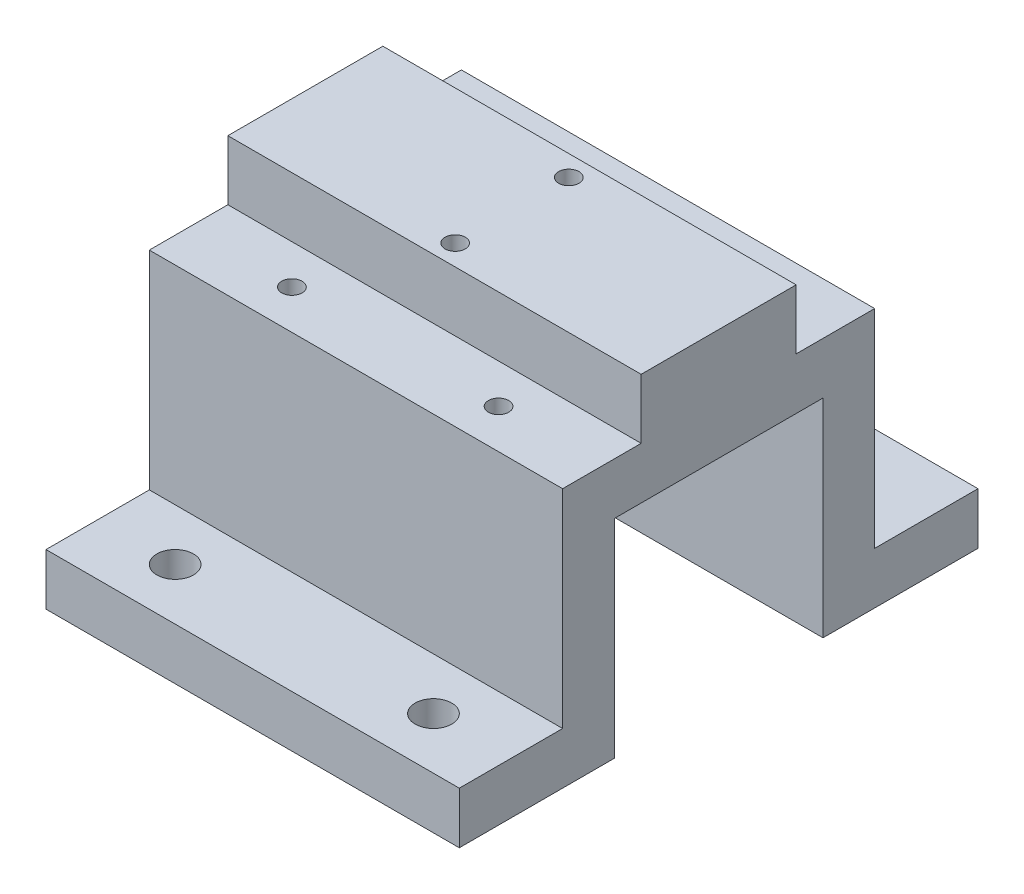
SolidWorks part; units mm, degrees
ref_plane "Front Plane" through (0, 0, 0) normal (0, 0, 1) x (1, 0, 0)
ref_plane "Top Plane" through (0, 0, 0) normal (0, 1, 0) x (1, 0, 0)
ref_plane "Right Plane" through (0, 0, 0) normal (1, 0, 0) x (0, 0, -1)
sketch "Sketch1" plane through (0, 0, 0) normal (1, 0, 0) x (0, 0, -1)
  line L0 (0, 0) -> (0, 51.054) construction
  line L1 (19.177, 31.877) -> (-19.177, 31.877)
  line L2 (-19.177, 31.877) -> (-19.177, 0)
  line L3 (-19.177, 0) -> (-12.827, 0)
  line L4 (-12.827, 0) -> (-12.827, 25.527)
  line L5 (-12.827, 25.527) -> (12.827, 25.527)
  line L6 (0, 25.527) -> (0, 31.877)
  line L7 (31.877, 0) -> (31.877, 6.35)
  line L8 (-19.177, 0) -> (-31.877, 0)
  line L9 (-19.177, 0) -> (-19.177, 6.35)
  line L10 (-19.177, 6.35) -> (-31.877, 6.35)
  line L11 (-31.877, 0) -> (-31.877, 6.35)
  line L12 (19.177, 6.35) -> (31.877, 6.35)
  line L13 (19.177, 0) -> (19.177, 6.35)
  line L14 (19.177, 0) -> (31.877, 0)
  line L15 (12.827, 0) -> (12.827, 25.527)
  line L16 (19.177, 0) -> (12.827, 0)
  line L17 (19.177, 31.877) -> (19.177, 0)
  dimension "D1" = 25.527
  dimension "D2" = 6.35
  dimension "D3" = 6.35
  dimension "D4" = 12.827
  dimension "D5" = 6.35
  dimension "D6" = 12.7
extrude "Boss-Extrude1" add sketch "Sketch1" along normal blind 50.8 contours L17 L1 L6 L5 L15 L16 L13 | L13 L14 L7 L12 | L5 L6 L1 L2 L3 L4 | L11 L8 L2 L10
sketch "Sketch2" plane through (0, 31.877, 0) normal (0, 1, 0) x (1, 0, 0)
  line L0 (0, 0) -> (50.8, 0) construction
  line L1 (0, 19.177) -> (0, -19.177) construction
  line L2 (50.8, 19.177) -> (50.8, -19.177) construction
  line L4 (50.8, -9.525) -> (0, -9.525)
  line L5 (50.8, -9.525) -> (50.8, 9.525)
  line L6 (50.8, 9.525) -> (0, 9.525)
  line L7 (0, -9.525) -> (0, 9.525)
  line L8 (50.8, -9.525) -> (0, 9.525) construction
  line L9 (50.8, 9.525) -> (0, -9.525) construction
  point P6 (25.4, 0)
  dimension "D1" = 19.05
extrude "Boss-Extrude2" add sketch "Sketch2" along normal blind 7.3508
hole_wizard "M3x0.5 Tapped Hole1" positions "Sketch3" profile "Sketch5" tap size "M3x0.5" standard "ANSI Metric"
sketch "Sketch3" plane through (0, 39.2278, 0) normal (0, 1, 0) x (1, 0, 0)
  line L1 (0, 0) -> (50.8, 0) construction
  line L2 (50.8, -9.525) -> (50.8, 9.525) construction
  line L4 (25.4, 6.985) -> (25.4, -6.985) construction
  point P10 (25.4, 6.985)
  point P11 (25.4, -6.985)
  point P15 (25.4, 0)
  dimension "D1" = 13.97
sketch "Sketch5" plane through (25.4, 39.2278, 6.985) normal (1, 0, 0) x (0, 0, 1)
  line L0 (0, 0) -> (0, 7.1011)
  line L1 (0, 7.1011) -> (1.25, 6.35)
  line L2 (1.25, 6.35) -> (1.25, 0)
  line L5 (1.25, 0) -> (0, 0)
  line L10 (0, 7.1011) -> (-1.25, 6.35) construction
  line L11 (0, -6.35) -> (0, 107.95) construction
  dimension "Tap Drill Dia." = 2.5
  dimension "Tap Drill Depth" = 6.35
  dimension "Drill Angle" = 118
cosmetic thread "Hole Thread1" parameters "D1"=6.096, "D2"=3
cosmetic thread "Hole Thread2" parameters "D1"=6.096, "D2"=3
hole_wizard "M3x0.5 Tapped Hole2" positions "Sketch6" profile "Sketch8" tap size "M3x0.5" standard "ANSI Metric" end condition through all
sketch "Sketch6" plane through (0, 31.877, 0) normal (0, 1, 0) x (1, 0, 0)
  line L0 (0, 14.351) -> (50.8, 14.351) construction
  line L1 (0, 19.177) -> (0, 9.525) construction
  line L2 (50.8, 19.177) -> (50.8, 9.525) construction
  point P9 (12.7, 14.351)
  point P11 (38.1, 14.351)
  dimension "D1" = 12.7
  dimension "D2" = 12.7
cosmetic thread "Hole Thread3" parameters "D2"=3
cosmetic thread "Hole Thread4" parameters "D2"=3
sketch "Sketch8" plane through (38.1, 31.877, -14.351) normal (1, 0, 0) x (0, 0, 1)
  line L0 (0, 0) -> (0, 31.877)
  line L1 (0, 31.877) -> (1.25, 31.877)
  line L2 (1.25, 31.877) -> (1.25, 0)
  line L5 (1.25, 0) -> (0, 0)
  line L11 (0, -6.35) -> (0, 107.95) construction
  dimension "Thru Tap Drill Dia." = 2.5
  dimension "Thru Tap Drill Depth" = 31.877
mirror "Mirror1" about plane through (0, 0, 0) normal (0, 0, 1) of "M3x0.5 Tapped Hole2"
cosmetic thread "Hole Thread5" parameters "D2"=3
cosmetic thread "Hole Thread6" parameters "D2"=3
hole_wizard "M4 Clearance Hole1" positions "Sketch9" profile "Sketch11" hole size "M4" standard "ANSI Metric" end condition through all
sketch "Sketch9" plane through (0, 6.35, 0) normal (0, 1, 0) x (1, 0, 0)
  line L0 (0, 25.527) -> (50.8, 25.527) construction
  line L1 (0, 19.177) -> (0, 31.877) construction
  line L2 (50.8, 19.177) -> (50.8, 31.877) construction
  point P9 (9.525, 25.527)
  point P11 (41.275, 25.527)
  dimension "D1" = 9.525
  dimension "D2" = 9.525
sketch "Sketch11" plane through (41.275, 6.35, -25.527) normal (1, 0, 0) x (0, 0, 1)
  line L0 (0, 0) -> (0, 6.35)
  line L1 (0, 6.35) -> (2.25, 6.35)
  line L2 (2.25, 6.35) -> (2.25, 0)
  line L5 (2.25, 0) -> (0, 0)
  line L11 (0, -6.35) -> (0, 107.95) construction
  dimension "Thru Hole Dia." = 4.5
  dimension "Thru Hole Depth" = 6.35
mirror "Mirror2" about plane through (0, 0, 0) normal (0, 0, 1) of "M4 Clearance Hole1"
